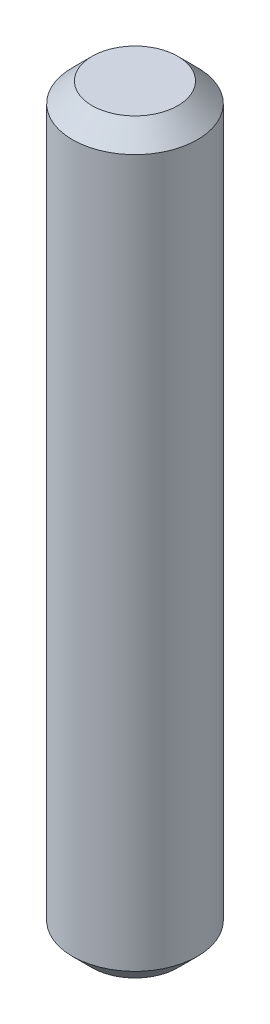
SolidWorks part; units mm, degrees
material "1023 Carbon Steel Sheet (SS)"
ref_plane "Front Plane" through (0, 0, 0) normal (0, 0, 1) x (1, 0, 0)
ref_plane "Top Plane" through (0, 0, 0) normal (0, 1, 0) x (1, 0, 0)
ref_plane "Right Plane" through (0, 0, 0) normal (1, 0, 0) x (0, 0, -1)
sketch "Sketch1" plane through (0, 0, 0) normal (0, 1, 0) x (1, 0, 0)
  circle A0 centre (0, 0) radius 1.59
  dimension "D1" = 3.18
extrude "Boss-Extrude1" add sketch "Sketch1" along normal mid plane 19
chamfer "Chamfer1" distance 0.5 angle 45 2 edges at (0, -9.5, 1.59) (0, 9.5, 1.59)
